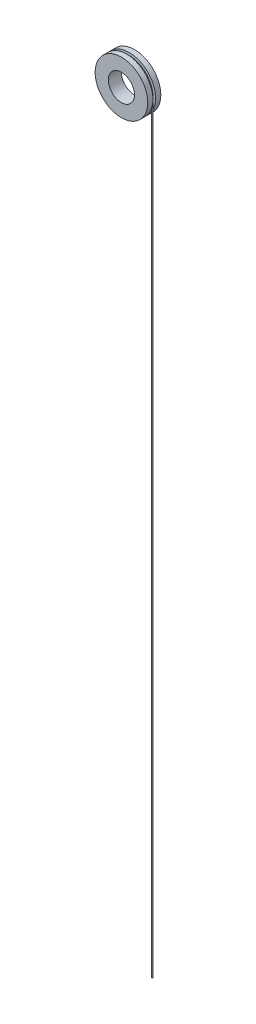
SolidWorks part; units mm, degrees
ref_plane "Front Plane" through (0, 0, 0) normal (0, 0, 1) x (1, 0, 0)
ref_plane "Top Plane" through (0, 0, 0) normal (0, 1, 0) x (1, 0, 0)
ref_plane "Right Plane" through (0, 0, 0) normal (1, 0, 0) x (0, 0, -1)
sketch "Sketch1" plane through (0, 0, 0) normal (0, 0, 1) x (1, 0, 0)
  circle A0 centre (0, 0) radius 5
  circle A1 centre (0, 0) radius 10
  dimension "D1" = 10
  dimension "D2" = 20
extrude "Boss-Extrude1" add sketch "Sketch1" along normal mid plane 5
sketch "Sketch2" plane through (0, 0, 0) normal (0, 0, 1) x (1, 0, 0)
  circle A0 centre (0, 0) radius 9
  circle A1 centre (0, 0) radius 10
  dimension "D1" = 18
  dimension "D2" = 20
extrude "Cut-Extrude1" cut sketch "Sketch2" against normal mid plane 1
sketch "Sketch3" plane through (0, 0, 0) normal (0, 0, 1) x (1, 0, 0)
  line L0 (9.25, 0) -> (9.25, -290)
  circle A0 centre (0, 0) radius 9.25
  dimension "D1" = 18.5
  dimension "D2" = 290
sketch "Sketch4" plane through (0, 0, 0) normal (0, 1, 0) x (1, 0, 0)
  circle A0 centre (9.25, 0) radius 0.25
  dimension "D1" = 0.5
sweep "Sweep1" add profiles "Sketch4" path "Sketch3"
